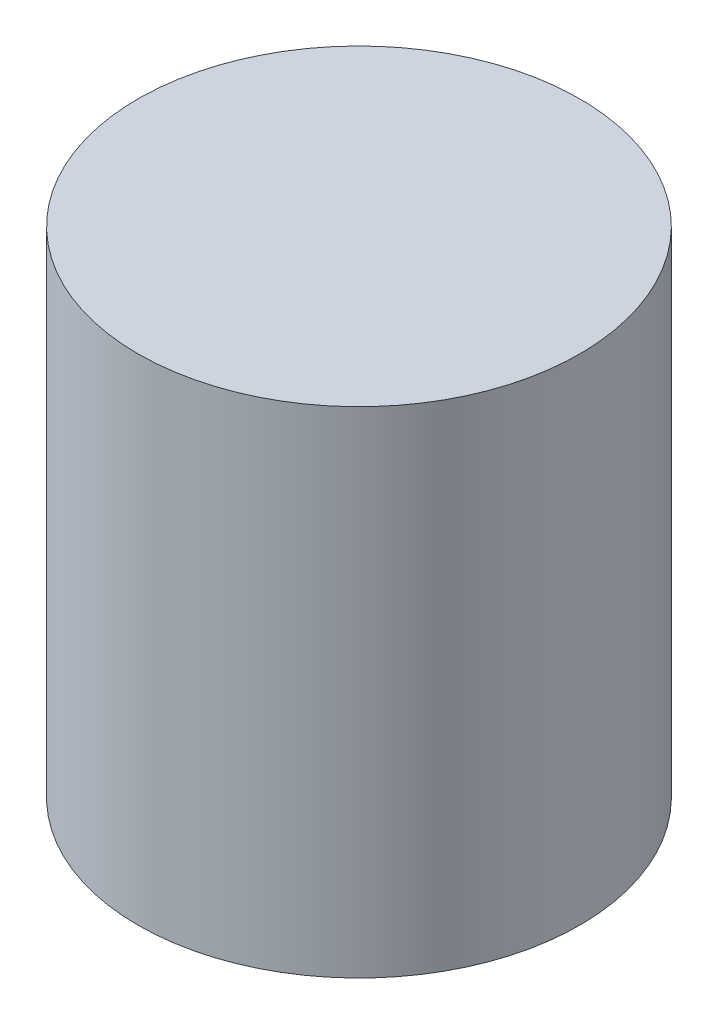
SolidWorks part; units mm, degrees
ref_plane "Front Plane" through (0, 0, 0) normal (0, 0, 1) x (1, 0, 0)
ref_plane "Top Plane" through (0, 0, 0) normal (0, 1, 0) x (1, 0, 0)
ref_plane "Right Plane" through (0, 0, 0) normal (1, 0, 0) x (0, 0, -1)
sketch "Sketch1" plane through (0, 0, 0) normal (0, 1, 0) x (1, 0, 0)
  circle A0 centre (0, 0) radius 6.35
extrude "Boss-Extrude1" add sketch "Sketch1" along normal blind 14.224 contours A0
